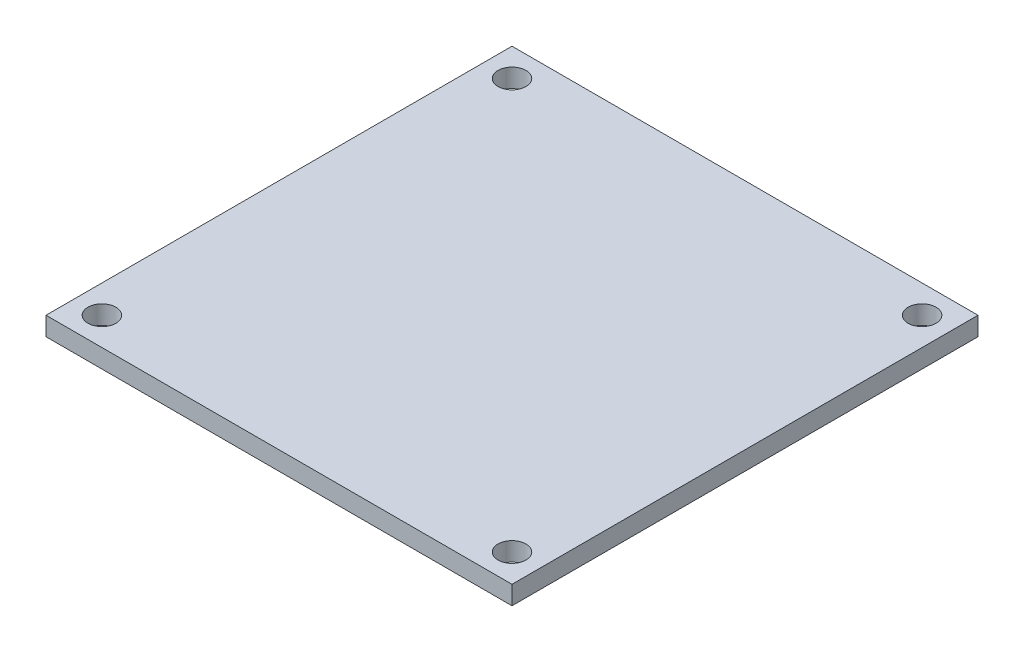
SolidWorks part; units mm, degrees
ref_plane "Alzado" through (0, 0, 0) normal (0, 0, 1) x (1, 0, 0)
ref_plane "Planta" through (0, 0, 0) normal (0, 1, 0) x (1, 0, 0)
ref_plane "Vista lateral" through (0, 0, 0) normal (1, 0, 0) x (0, 0, -1)
sketch "Croquis1" plane through (0, 0, 0) normal (0, 1, 0) x (1, 0, 0)
  line L0 (31.9561, 282.4162) -> (355.2402, 288.0591) construction
  line L1 (-60, -25) -> (-10, -25)
  line L2 (-60, -25) -> (-60, 25)
  line L3 (-60, 25) -> (-10, 25)
  line L5 (-60, -25) -> (-10, -4.1667) construction
  line L6 (-60, 25) -> (-10, 4.1667) construction
  line L7 (-10, 25) -> (-10, -25)
  circle A3 centre (-57, -22) radius 1.5
  circle A4 centre (-13, -22) radius 1.5
  circle A5 centre (-13, 22) radius 1.5
  circle A6 centre (-57, 22) radius 1.5
  point P0 (0, 0)
  dimension "D4" = 3
  dimension "D1" = 50
  dimension "D2" = 50
  dimension "D3" = 3
  dimension "D5" = 3
  dimension "D6" = 2
  dimension "D7" = 2
extrude "Saliente-Extruir4" add sketch "Croquis1" along normal blind 2 contours L1 L7 L3 L2
